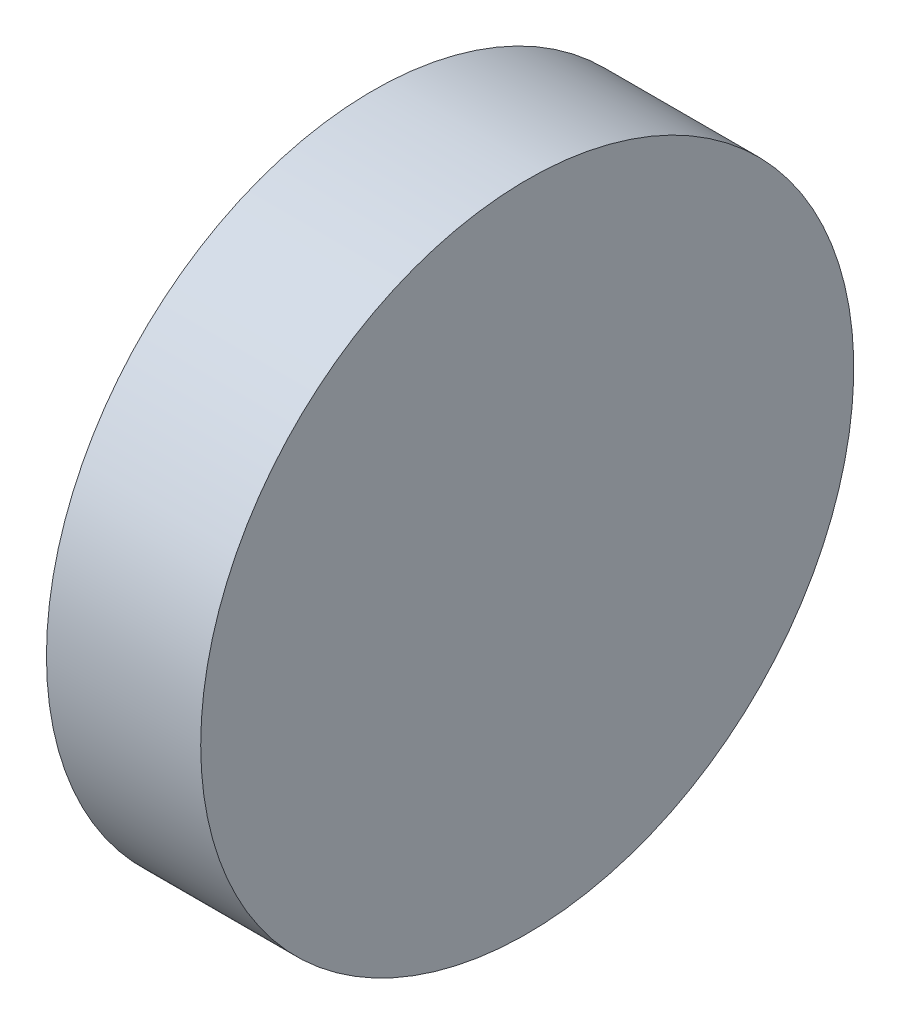
SolidWorks part; units mm, degrees
ref_plane "前视基准面" through (0, 0, 0) normal (0, 0, 1) x (1, 0, 0)
ref_plane "上视基准面" through (0, 0, 0) normal (0, 1, 0) x (1, 0, 0)
ref_plane "右视基准面" through (0, 0, 0) normal (1, 0, 0) x (0, 0, -1)
sketch "草图1" plane through (0, 0, 0) normal (0, 0, 1) x (1, 0, 0)
  line L0 (0, 6.35) -> (0, 0)
  line L2 (0, 6.35) -> (3, 6.35)
  line L3 (0, 0) -> (3, 0)
  line L4 (3, 6.35) -> (3, 0)
  dimension "D1" = 6.35
  dimension "D2" = 3
revolve "旋转2" add sketch "草图1" angle 360 about L3
